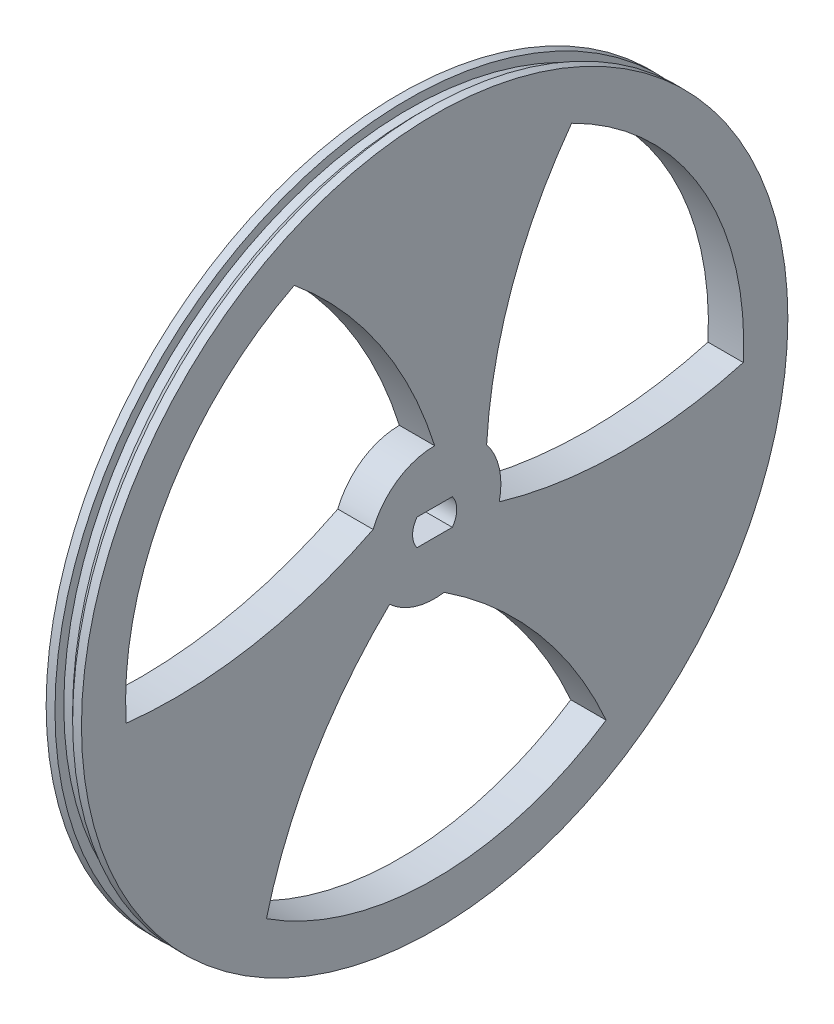
SolidWorks part; units mm, degrees
ref_plane "Front Plane" through (0, 0, 0) normal (0, 0, 1) x (1, 0, 0)
ref_plane "Top Plane" through (0, 0, 0) normal (0, 1, 0) x (1, 0, 0)
ref_plane "Right Plane" through (0, 0, 0) normal (1, 0, 0) x (0, 0, -1)
sketch "Sketch2" plane through (0, 0, 0) normal (1, 0, 0) x (0, 0, -1)
  line L0 (-2, 1.5) -> (2, 1.5)
  line L1 (2, -1.5) -> (-2, -1.5)
  circle A0 centre (0, 0) radius 40
  arc A1 (-15.9029, 31.1785) -> (-34.9274, -2.253) centre (0, 0) ccw
  arc A2 (0, 7.5) -> (-6.9683, 2.7736) centre (0, 0) ccw
  arc A3 (5.8861, 4.6479) -> (15.5125, 31.3745) centre (55.803, 1.7658) cw
  arc A5 (1.0822, -7.4215) -> (19.4149, -29.1215) centre (-26.3722, -49.2098) cw
  arc A6 (7.3131, -1.664) -> (34.9528, -1.8169) centre (21.3988, 46.3109) ccw
  arc A7 (-6.9683, 2.7736) -> (-34.9274, -2.253) centre (-29.4308, 47.4439) cw
  arc A8 (-5.0976, -5.5013) -> (-19.0499, -29.3616) centre (29.407, -41.6874) ccw
  arc A9 (34.9528, -1.8169) -> (15.5125, 31.3745) centre (0, 0) ccw
  arc A10 (-19.0499, -29.3616) -> (19.4149, -29.1215) centre (0, 0) ccw
  arc A11 (0, 7.5) -> (-15.9029, 31.1785) centre (-47.7346, -7.3798) ccw
  arc A12 (7.3131, -1.664) -> (5.8861, 4.6479) centre (0, 0) ccw
  arc A13 (-5.0976, -5.5013) -> (1.0822, -7.4215) centre (0, 0) ccw
  arc A15 (-2, 1.5) -> (-2, -1.5) centre (0, 0) ccw
  arc A16 (2, -1.5) -> (2, 1.5) centre (0, 0) ccw
  point P20 (0, 0)
  dimension "D1" = 80
  dimension "D2" = 5
  dimension "D3" = 50
  dimension "D4" = 5
  dimension "D6" = 15
  dimension "D5" = 3
  dimension "D7" = 3
extrude "Boss-Extrude1" add sketch "Sketch2" along normal blind 4
sketch "Sketch3" plane through (0, 0, 0) normal (0, 0, 1) x (1, 0, 0)
  line L0 (-1.5991, 0) -> (6.8857, 0) construction
  line L1 (4, 40) -> (0, 40) construction
  line L2 (1, 40) -> (3, 40)
  line L3 (1, 40) -> (1, 39)
  line L4 (1, 39) -> (3, 39)
  line L5 (3, 40) -> (3, 39)
  line L8 (4, -40) -> (4, 40) construction
  dimension "D1" = 1
  dimension "D2" = 2
  dimension "D3" = 1
revolve "Cut-Revolve1" cut sketch "Sketch3" angle 360 about L0
sketch "Sketch4" plane through (0, 0, 0) normal (0, 0, 1) x (1, 0, 0)
  line L0 (0, 0) -> (10.4984, 0) construction
  line L1 (3, 40) -> (2, 39)
  line L2 (2, 39) -> (3, 39)
  line L3 (3, 39) -> (3, 40)
  line L4 (3, 40) -> (3, -40) construction
  point P10 (0, 0)
  dimension "D1" = 1
  dimension "D2" = 1
  dimension "D3" = 39
revolve "Revolve1" add sketch "Sketch4" angle 360 about L0
